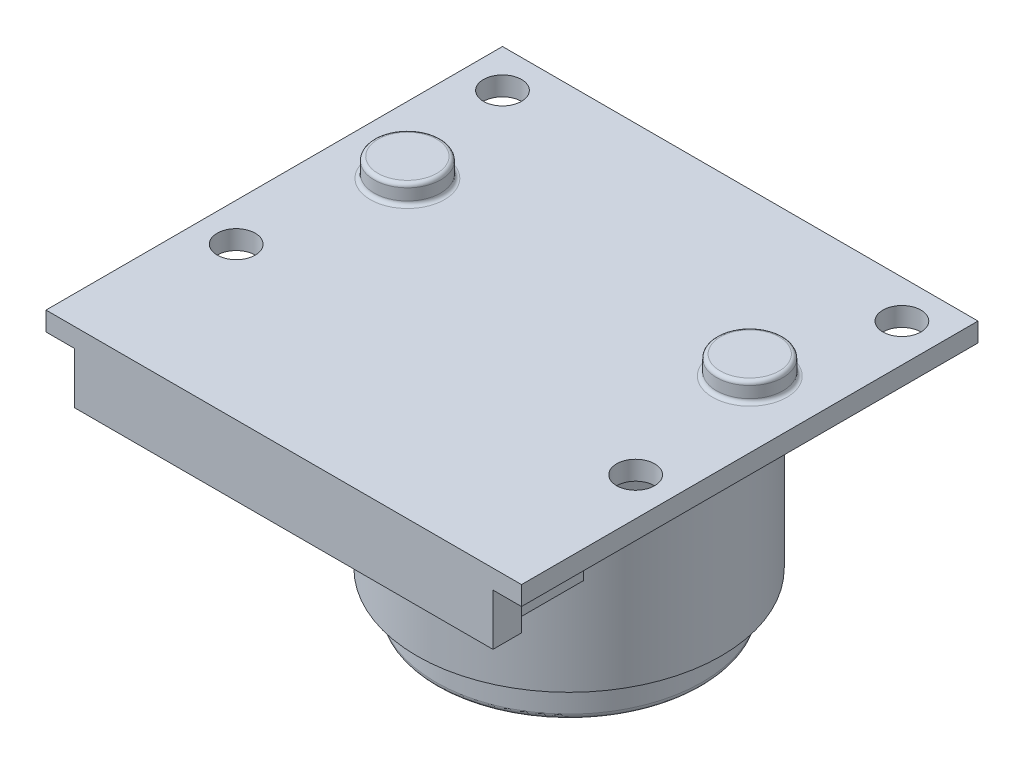
SolidWorks part; units mm, degrees
ref_plane "Спереди" through (0, 0, 0) normal (0, 0, 1) x (1, 0, 0)
ref_plane "Сверху" through (0, 0, 0) normal (0, 1, 0) x (1, 0, 0)
ref_plane "Справа" through (0, 0, 0) normal (1, 0, 0) x (0, 0, -1)
sketch "Эскиз1" plane through (0, 0, 0) normal (0, 1, 0) x (1, 0, 0)
  line L1 (12.5, -12) -> (-12.5, -12)
  line L2 (12.5, -12) -> (12.5, 12)
  line L3 (12.5, 12) -> (-12.5, 12)
  line L4 (-12.5, -12) -> (-12.5, 12)
  line L5 (12.5, -12) -> (-12.5, 12) construction
  line L6 (12.5, 12) -> (-12.5, -12) construction
  circle A0 centre (-10.5, 10) radius 1
  circle A1 centre (10.5, 10) radius 1
  circle A2 centre (10.5, -4) radius 1
  circle A3 centre (-10.5, -4) radius 1
  point P0 (0, 0)
  dimension "D3" = 2
  dimension "D1" = 25
  dimension "D2" = 24
  dimension "D4" = 21
  dimension "D5" = 10.5
  dimension "D6" = 14
  dimension "D7" = 2
extrude "Бобышка-Вытянуть1" add sketch "Эскиз1" along normal blind 1
sketch "Эскиз2" plane through (0, 1, 0) normal (0, 1, 0) x (1, 0, 0)
  line L0 (12.5, 12) -> (-12.5, 12) construction
  circle A0 centre (-9, 3.5) radius 1.75
  circle A1 centre (9, 3.5) radius 1.75
  dimension "D1" = 3.5
  dimension "D2" = 18
  dimension "D3" = 9
  dimension "D4" = 8.5
extrude "Бобышка-Вытянуть2" add sketch "Эскиз2" along normal blind 1
fillet "Скругление1" radius 0.2 4 edges at (9, 1, -1.75) (9, 2, -1.75) (-9, 1, -1.75) (-9, 2, -1.75)
sketch "Эскиз3" plane through (0, 0, 0) normal (0, -1, 0) x (1, 0, 0)
  line L0 (-12.5, 12) -> (12.5, 12) construction
  line L1 (-10.25, 6.5) -> (10.25, 6.5)
  line L2 (-10.25, 6.5) -> (-10.25, 10.5)
  line L3 (-10.25, 10.5) -> (10.25, 10.5)
  line L4 (10.25, 6.5) -> (10.25, 10.5)
  line L5 (-10.25, 6.5) -> (10.25, 10.5) construction
  line L6 (-10.25, 10.5) -> (10.25, 6.5) construction
  line L7 (-11, 10.5) -> (11, 10.5)
  line L8 (-11, 10.5) -> (-11, 12)
  line L9 (-11, 12) -> (11, 12)
  line L10 (11, 10.5) -> (11, 12)
  line L11 (-11, 10.5) -> (11, 12) construction
  line L12 (-11, 12) -> (11, 10.5) construction
  point P0 (0, 8.5)
  point P5 (0, 11.25)
  line M9 (12.5, 12) -> (-12.5, 12)
  dimension "D1" = 20.5
  dimension "D2" = 4
  dimension "D3" = 22
  dimension "D4" = 1.5
extrude "Бобышка-Вытянуть3" add sketch "Эскиз3" along normal blind 2.7 contours L1 L4 L3 L2 | L7 L10 L8 L3 M9
sketch "Эскиз4" plane through (0, 0, 0) normal (0, -1, 0) x (1, 0, 0)
  line L0 (12.5, -12) -> (-12.5, -12) construction
  circle A0 centre (0, -3) radius 8
  dimension "D1" = 16
  dimension "D2" = 9
extrude "Бобышка-Вытянуть4" add sketch "Эскиз4" along normal blind 12
sketch "Эскиз5" plane through (0, -12, 0) normal (0, -1, 0) x (1, 0, 0)
  circle A0 centre (0, -3) radius 7
  dimension "D1" = 14
extrude "Бобышка-Вытянуть5" add sketch "Эскиз5" along normal blind 2
fillet "Скругление2" radius 0.3 1 edges at (0, -14, -10)
sketch "Эскиз7" [suppressed] plane through (0, 0, 0) normal (1, 0, 0) x (0, 0, -1)
  line L0 (3.5, 1.2) -> (41.2597, -79.776)
  line L1 (1.75, 1.2) -> (5.25, 1.2) construction
  line L2 (41.2597, -79.776) -> (-34.2597, -79.776)
  line L3 (-34.2597, -79.776) -> (3.5, 1.2)
  point P4 (3.5, -79.776)
  dimension "D1" = 50
